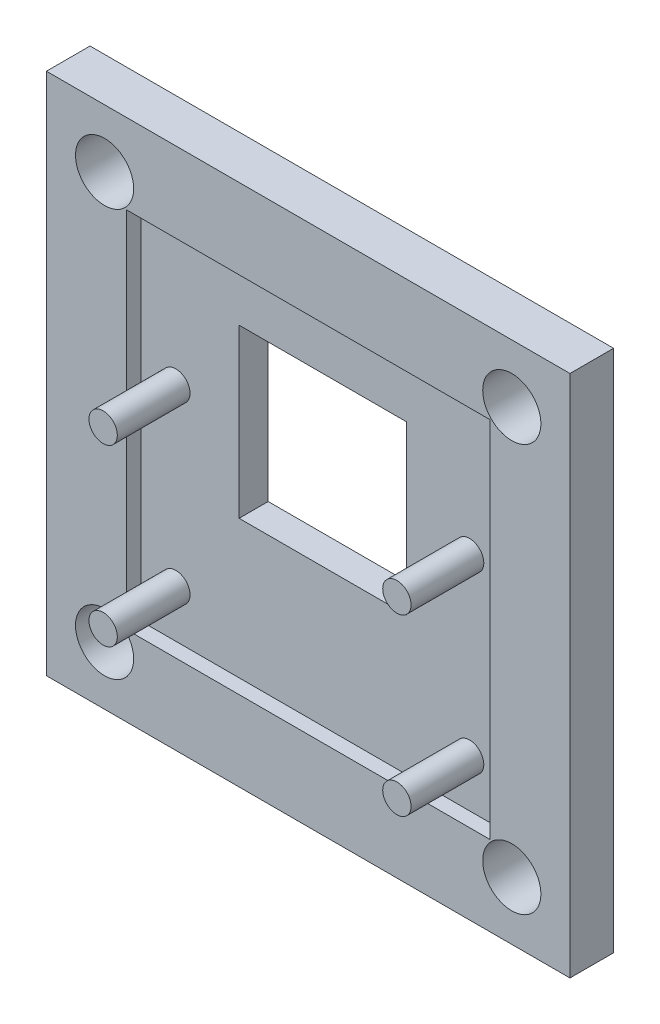
SolidWorks part; units mm, degrees
ref_plane "Front Plane" through (0, 0, 0) normal (0, 0, 1) x (1, 0, 0)
ref_plane "Top Plane" through (0, 0, 0) normal (0, 1, 0) x (1, 0, 0)
ref_plane "Right Plane" through (0, 0, 0) normal (1, 0, 0) x (0, 0, -1)
sketch "Sketch1" plane through (0, 0, 0) normal (0, 0, 1) x (1, 0, 0)
  line L1 (-18, -18) -> (18, -18)
  line L2 (-18, -18) -> (-18, 18)
  line L3 (-18, 18) -> (18, 18)
  line L4 (18, -18) -> (18, 18)
  line L5 (-18, -18) -> (18, 18) construction
  line L6 (-18, 18) -> (18, -18) construction
  point P0 (0, 0)
  dimension "D1" = 36
  dimension "D2" = 36
extrude "Boss-Extrude1" add sketch "Sketch1" along normal blind 3
sketch "Sketch5" plane through (0, 0, 3) normal (0, 0, 1) x (1, 0, 0)
  line L0 (-18, 18) -> (-18, -18) construction
  line L1 (18, 18) -> (-18, 18) construction
  line L2 (0, 0) -> (0, -1.9329) construction
  line L3 (0, -1.9329) -> (0, 0) construction
  line L4 (0, 0) -> (-2.2592, 0) construction
  circle A0 centre (-14, 14) radius 2
  circle A1 centre (-14, -14) radius 2
  circle A2 centre (14, -14) radius 2
  circle A3 centre (14, 14) radius 2
  dimension "D2" = 4
  dimension "D1" = 4
  dimension "D3" = 4
extrude "Cut-Extrude3" cut sketch "Sketch5" against normal blind 10
sketch "Sketch2" plane through (0, 0, 3) normal (0, 0, 1) x (1, 0, 0)
  line L1 (-12.5, -12.5) -> (12.5, -12.5)
  line L2 (-12.5, -12.5) -> (-12.5, 12.5)
  line L3 (-12.5, 12.5) -> (12.5, 12.5)
  line L4 (12.5, -12.5) -> (12.5, 12.5)
  line L5 (-12.5, -12.5) -> (12.5, 12.5) construction
  line L6 (-12.5, 12.5) -> (12.5, -12.5) construction
  point P0 (0, 0)
  dimension "25" = 25
  dimension "D2" = 25
extrude "Cut-Extrude1" cut sketch "Sketch2" against normal blind 1
sketch "Sketch4" plane through (0, 0, 2) normal (0, 0, 1) x (1, 0, 0)
  line L0 (0, 0) -> (0, -2.3847) construction
  line L5 (12.5, 12.5) -> (-12.5, 12.5) construction
  line L6 (-5.75, -3) -> (5.75, -3)
  line L7 (-5.75, -3) -> (-5.75, 8.5)
  line L8 (-5.75, 8.5) -> (5.75, 8.5)
  line L9 (5.75, -3) -> (5.75, 8.5)
  line L10 (-5.75, -3) -> (5.75, 8.5) construction
  line L11 (-5.75, 8.5) -> (5.75, -3) construction
  point P2 (0, 2.75)
  point P11 (0, 0)
  dimension "D1" = 11.5
  dimension "D2" = 4
  dimension "D3" = 11.5
extrude "Cut-Extrude4" cut sketch "Sketch4" against normal through all
sketch "Sketch3" plane through (0, 0, 2) normal (0, 0, 1) x (1, 0, 0)
  line L3 (-5.75, 2.75) -> (5.75, 2.75) construction
  line L5 (-5.75, 8.5) -> (-5.75, -3) construction
  line L6 (5.75, -3) -> (5.75, 8.5) construction
  line L7 (0, 2.75) -> (0, 4.4896) construction
  circle A4 centre (10.1, 2.75) radius 0.975
  circle A5 centre (10.1, -9.25) radius 0.975
  circle A6 centre (-10.1, -9.25) radius 0.975
  circle A7 centre (-10.1, 2.75) radius 0.975
  point P9 (0, 2.75)
  dimension "D1" = 10.1
  dimension "D3" = 1.95
  dimension "D2" = 1.95
  dimension "D4" = 12
extrude "Boss-Extrude2" add sketch "Sketch3" along normal blind 5
